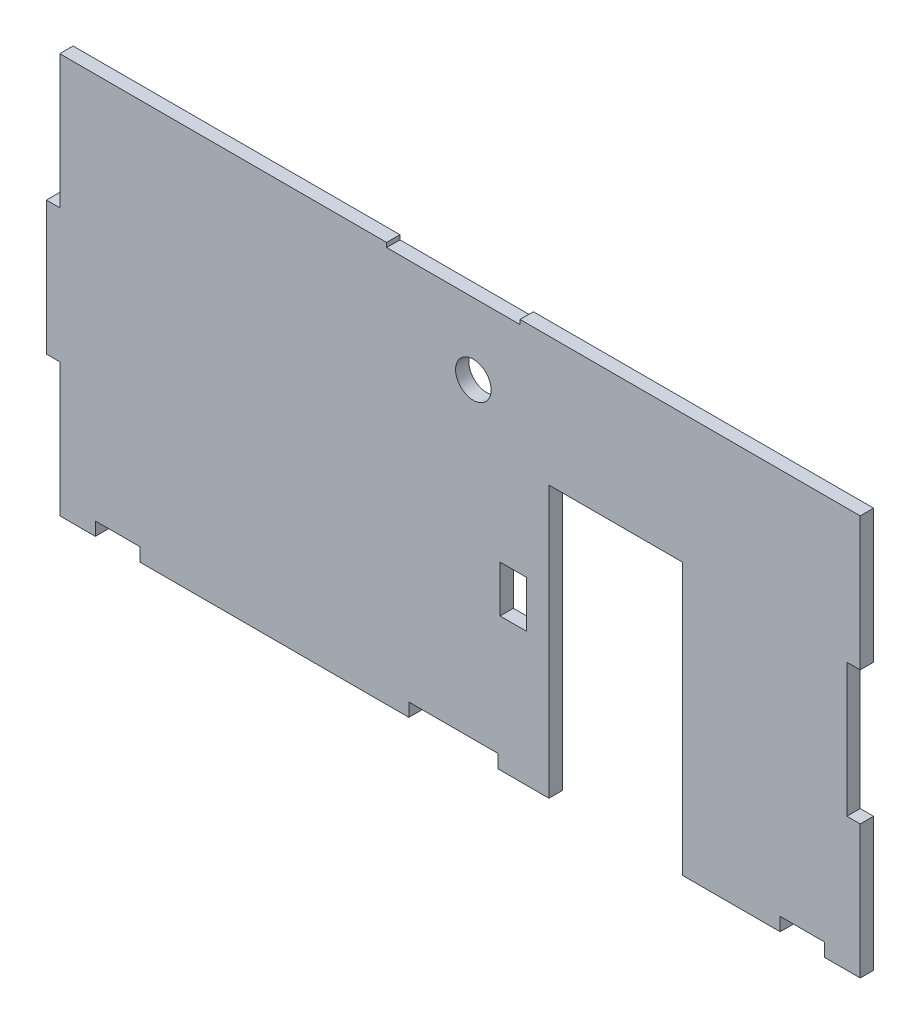
SolidWorks part; units mm, degrees
ref_plane "Front Plane" through (0, 0, 0) normal (0, 0, 1) x (1, 0, 0)
ref_plane "Top Plane" through (0, 0, 0) normal (0, 1, 0) x (1, 0, 0)
ref_plane "Right Plane" through (0, 0, 0) normal (1, 0, 0) x (0, 0, -1)
sketch "Model" plane through (0, 0, 0) normal (0, 0, 1) x (1, 0, 0)
  line L2 (-215.7427, 39.2755) -> (-157.2427, 39.2755)
  line L4 (-215.7427, 39.2755) -> (-217.7427, 39.2755)
  line L10 (-58.7427, 99.2755) -> (-55.7427, 99.2755)
  line L12 (-55.7427, 69.2755) -> (-58.7427, 69.2755)
  line L13 (-58.7427, 69.2755) -> (-58.7427, 99.2755)
  line L14 (-162.2427, 129.2755) -> (-162.2427, 128.2755)
  line L15 (-162.2427, 128.2755) -> (-132.2427, 128.2755)
  line L16 (-132.2427, 128.2755) -> (-132.2427, 129.2755)
  line L17 (-162.2427, 129.2755) -> (-235.7427, 129.2755)
  line L18 (-73.7427, 39.2755) -> (-95.7427, 39.2755)
  line L19 (-137.2427, 39.2755) -> (-125.7427, 39.2755)
  line L21 (-55.7427, 99.2755) -> (-55.7427, 129.2755)
  line L22 (-55.7427, 69.2755) -> (-55.7427, 39.2755)
  line L23 (-136.7427, 79.7755) -> (-130.7427, 79.7755)
  line L37 (-63.7427, 39.2755) -> (-55.7427, 39.2755)
  line L65 (-55.7427, 129.2755) -> (-132.2427, 129.2755)
  line L91 (-235.7427, 69.2755) -> (-238.7427, 69.2755)
  line L92 (-238.7427, 69.2755) -> (-238.7427, 99.2755)
  line L93 (-238.7427, 99.2755) -> (-235.7427, 99.2755)
  line L94 (-235.7427, 99.2755) -> (-235.7427, 129.2755)
  line L98 (-235.7427, 69.2755) -> (-235.7427, 39.2755)
  line L99 (-136.7427, 79.7755) -> (-136.7427, 69.2755)
  line L100 (-136.7427, 69.2755) -> (-130.7427, 69.2755)
  line L101 (-130.7427, 79.7755) -> (-130.7427, 69.2755)
  line L102 (-136.7427, 79.7755) -> (-130.7427, 69.2755) construction
  line L103 (-136.7427, 69.2755) -> (-130.7427, 79.7755) construction
  line L104 (-227.7427, 42.2755) -> (-217.7427, 42.2755)
  line L105 (-217.7427, 42.2755) -> (-217.7427, 39.2755)
  line L106 (-227.7427, 42.2755) -> (-227.7427, 39.2755)
  line L107 (-235.7427, 39.2755) -> (-227.7427, 39.2755)
  line L108 (-63.7427, 39.2755) -> (-63.7427, 42.2755)
  line L109 (-63.7427, 42.2755) -> (-73.7427, 42.2755)
  line L110 (-73.7427, 42.2755) -> (-73.7427, 39.2755)
  line L111 (-157.2427, 39.2755) -> (-157.2427, 42.2755)
  line L112 (-157.2427, 42.2755) -> (-137.2427, 42.2755)
  line L113 (-137.2427, 42.2755) -> (-137.2427, 39.2755)
  line L118 (-125.7427, 39.2755) -> (-125.7427, 100.2755)
  line L119 (-125.7427, 100.2755) -> (-95.7427, 100.2755)
  line L120 (-95.7427, 100.2755) -> (-95.7427, 39.2755)
  circle A1 centre (-142.7427, 112.2755) radius 4
  point P30 (-133.7427, 74.5255)
  dimension "D19" = 30
  dimension "D4" = 180
  dimension "D5" = 30
  dimension "D6" = 93
  dimension "D29" = 73
  dimension "D3" = 8
  dimension "D7" = 76.5
  dimension "D8" = 90
  dimension "D9" = 3
  dimension "D10" = 6
  dimension "D11" = 8
  dimension "D12" = 10.5
  dimension "D13" = 40
  dimension "D14" = 5
  dimension "D15" = 10
  dimension "D16" = 30
  dimension "D17" = 30
  dimension "D18" = 8
  dimension "D20" = 10
  dimension "D21" = 11.5
  dimension "D22" = 3
  dimension "D23" = 20
  dimension "D24" = 61
  dimension "D25" = 3
  dimension "D26" = 1
  dimension "D27" = 30
extrude "Boss-Extrude1" add sketch "Model" along normal blind 3
